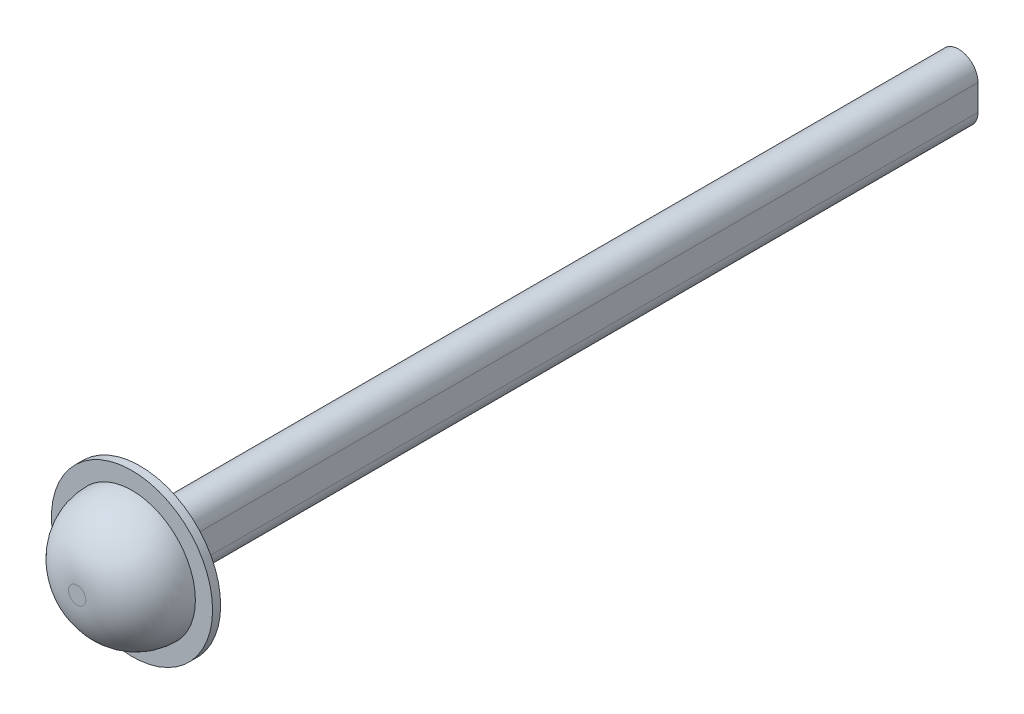
SolidWorks part; units mm, degrees
other "标注1"
sketch "草图5" plane through (20, -20, 198.9919) normal (0.0528, -0.7701, 0.6357) x (0.5314, -0.5173, -0.6708)
ref_plane "前视基准面" through (0, 0, 0) normal (0, 0, 1) x (1, 0, 0)
ref_plane "上视基准面" through (0, 0, 0) normal (0, 1, 0) x (1, 0, 0)
ref_plane "右视基准面" through (0, 0, 0) normal (1, 0, 0) x (0, 0, -1)
sketch "草图1" plane through (0, 0, 0) normal (0, 0, 1) x (1, 0, 0)
  line L0 (0, -8.2718) -> (0, 30.2718) construction
  point P1 (0, 0)
sketch "草图2" plane through (0, 0, 0) normal (0, 0, 1) x (1, 0, 0)
  line L0 (0, 4) -> (0, -4) construction
  line L1 (0, -200008.2718) -> (0, 200030.2718) construction
  line L2 (6, 4) -> (6, -4)
  line L3 (-6, 4) -> (-6, -4)
  arc A0 (6, 4) -> (-6, 4) centre (0, 4) ccw
  arc A1 (-6, -4) -> (6, -4) centre (0, -4) ccw
  point P5 (0, 0)
  dimension "D1" = 6
  dimension "D2" = 8
extrude "凸台-拉伸1" add sketch "草图2" along normal blind 254
sketch "草图3" plane through (0, 0, 254) normal (0, 0, 1) x (1, 0, 0)
  circle A0 centre (0, 0) radius 25
  dimension "D1" = 50
extrude "凸台-拉伸2" add sketch "草图3" along normal blind 2.5
chamfer "倒角1" distance 3 angle 45 4 edges at (6, 0, 254) (0, 10, 254) (0, -10, 254) (-6, 0, 254)
sketch "草图4" plane through (0, 0, 0) normal (1, 0, 0) x (0, 0, -1)
  line L0 (-256.5, 0) -> (-256.5, -19.6696)
  line L1 (-256.5, 25) -> (-256.5, -25) construction
  line L2 (-273.5, -2.6696) -> (-273.5, 0)
  line L3 (-273.5, 0) -> (-256.5, 0)
  line L4 (0, -4) -> (0, 4) construction
  arc A0 (-256.5, -19.6696) -> (-273.5, -2.6696) centre (-256.5, -2.6696) cw
  point P6 (-272.5, -2.6696)
  dimension "D2" = 273.5
revolve "旋转1" add sketch "草图4" angle 360 about L3
